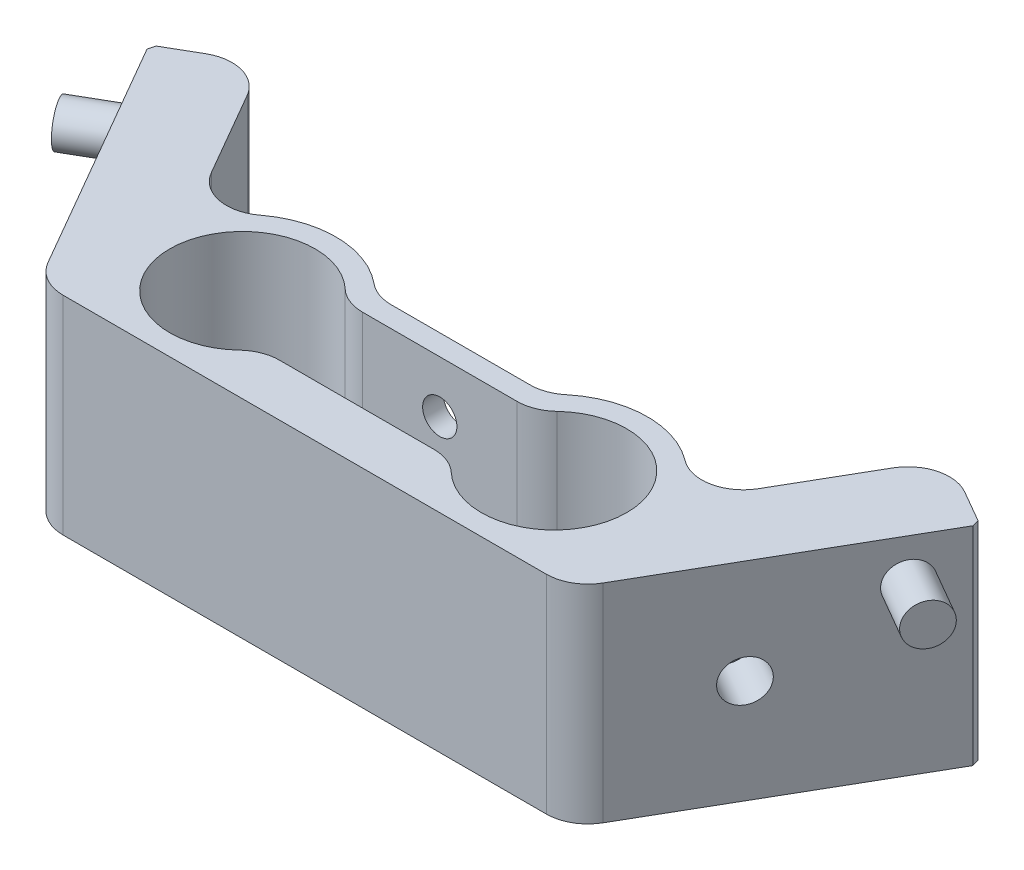
SolidWorks part; units mm, degrees
material "Сплав 2024"
ref_plane "Спереди" through (0, 0, 0) normal (0, 0, 1) x (1, 0, 0)
ref_plane "Сверху" through (0, 0, 0) normal (0, 1, 0) x (1, 0, 0)
ref_plane "Справа" through (0, 0, 0) normal (1, 0, 0) x (0, 0, -1)
sketch "Эскиз1" plane through (0, 0, 0) normal (0, 1, 0) x (1, 0, 0)
  line L0 (0, 0) -> (14.4338, -25)
  line L1 (14.4338, -25) -> (65.5662, -25)
  line L2 (65.5662, -25) -> (80, 0)
  line L3 (80, 0) -> (73.0718, 4)
  line L4 (73.0718, 4) -> (63.3961, -12.7588)
  line L5 (31.7082, -10) -> (48.2918, -10)
  line L6 (16.6039, -12.7588) -> (6.9282, 4)
  line L7 (6.9282, 4) -> (0, 0)
  line L8 (0, 5.2504) -> (0, -36.0928) construction
  line L9 (80, 1.6052) -> (80, -36.8181) construction
  line L10 (40, -7) -> (40, -25) construction
  line L11 (40, -16) -> (80, -16) construction
  line L12 (40, -16) -> (0, -16) construction
  line L13 (25, -16) -> (25, -18.6268) construction
  line L14 (55, -16) -> (55, -18.6268) construction
  circle A0 centre (25, -16) radius 7 construction
  circle A1 centre (55, -16) radius 7 construction
  circle A2 centre (55, -16) radius 9 construction
  circle A3 centre (25, -16) radius 9 construction
  arc A4 (16.6039, -12.7588) -> (31.7082, -10) centre (25, -16) cw
  arc A5 (48.2918, -10) -> (63.3961, -12.7588) centre (55, -16) cw
  dimension "D6" = 14
  dimension "D7" = 14
  dimension "D8" = 15
  dimension "D15" = 9
  dimension "D16" = 9
  dimension "D9" = 2
  dimension "D17" = 15
  dimension "D1" = 80
  dimension "D2" = 30
  dimension "D3" = 30
  dimension "D4" = 8
  dimension "D5" = 8
  dimension "D10" = 15
  dimension "D11" = 9
  dimension "D12" = 2
  dimension "D13" = 25
  dimension "D14" = 40
extrude "Бобышка-Вытянуть1" add sketch "Эскиз1" along normal blind 20
sketch "Эскиз2" plane through (0, 20, 0) normal (0, 1, 0) x (1, 0, 0)
  line L1 (40, -16) -> (0, -16) construction
  line L2 (25, -16) -> (25, -18.6268) construction
  circle A0 centre (25, -16) radius 7
  circle A1 centre (55, -16) radius 7
  dimension "D1" = 14
extrude "Вырез-Вытянуть1" cut sketch "Эскиз2" against normal through all
sketch "Эскиз3" plane through (0, 20, 0) normal (0, 1, 0) x (1, 0, 0)
  line L0 (40, -7) -> (40, -25) construction
  line L1 (25, -12) -> (55, -12)
  line L2 (25, -12) -> (25, -20)
  line L3 (25, -20) -> (55, -20)
  line L4 (55, -12) -> (55, -20)
  line L5 (25, -12) -> (55, -20) construction
  line L6 (25, -20) -> (55, -12) construction
  line L8 (25, -16) -> (25, -18.6268) construction
  point P0 (40, -16)
  dimension "D1" = 8
extrude "Вырез-Вытянуть2" cut sketch "Эскиз3" against normal through all
fillet "Скругление1" radius 4 12 edges at (49.2554, 10, 12) (30.7446, 10, 12) (30.7446, 10, 20) (49.2554, 10, 20) (48.2918, 10, 10) (31.7082, 10, 10) (6.9282, 10, -4) (73.0718, 10, -4) (14.4338, 10, 25) (65.5662, 10, 25) (63.3961, 10, 12.7588) (16.6039, 10, 12.7588)
chamfer "Фаска1" distance 0.5 angle 45 2 edges at (80, 10, 0) (0, 10, 0)
sketch "Эскиз4" plane through (0, 0, 10) normal (0, 0, -1) x (-1, 0, 0)
  line L0 (-40, 20) -> (-40, 0) construction
  line L1 (-46.6934, 20) -> (-33.3066, 20) construction
  line L2 (-40, 0) -> (-80, 0) construction
  line L3 (-46.6934, 15) -> (-33.3066, 15) construction
  line L4 (-46.6934, 20) -> (-46.6934, 0) construction
  line L5 (-33.3066, 0) -> (-33.3066, 20) construction
  line L6 (-46.6934, 5) -> (-33.3066, 5) construction
  line L7 (-40, 0) -> (0, 0) construction
  dimension "D1" = 5
  dimension "D2" = 5
hole_wizard "Отверстие обработанное метчиком M4x0.71" positions "Трехмерный эскиз1" profile "Эскиз5" tap size "M4x0.7" standard "Ansi Metric"
sketch3d "Трехмерный эскиз1"
  line L0 (46.6934, 15, 10) -> (33.3066, 15, 10) construction
  line L1 (46.6934, 5, 10) -> (33.3066, 5, 10) construction
  line L2 (40, 20, 10) -> (40, 0, 10) construction
  point P8 (40, 5, 10)
  point P12 (40, 15, 10)
sketch "Эскиз5" plane through (40, 5, 10) normal (1, 0, 0) x (0, 1, 0)
  line L0 (0, 0) -> (0, 14.4914)
  line L1 (0, 14.4914) -> (1.65, 13.5)
  line L2 (1.65, 13.5) -> (1.65, 0)
  line L5 (1.65, 0) -> (0, 0)
  line L10 (0, 14.4914) -> (-1.65, 13.5) construction
  line L11 (0, -6.35) -> (0, 107.95) construction
  dimension "Диаметр сверла" = 3.3
  dimension "Глубина сверла" = 13.5
  dimension "Угол заточки сверла" = 118
sketch "Эскиз6" plane through (60, 0, 34.641) normal (0.866, 0, 0.5) x (0.5, 0, -0.866)
  line L0 (33.4419, 20) -> (33.4419, 0) construction
  line L1 (13.4419, 20) -> (39.5, 20) construction
  line L2 (13.4419, 0) -> (39.5, 0) construction
  line L3 (13.4419, 20) -> (13.4419, 0) construction
  line L4 (40, 20) -> (40, 0) construction
  line L5 (40, 10) -> (13.4419, 10) construction
  line L6 (23.4419, 20) -> (23.4419, 0) construction
  circle A0 centre (23.4419, 10) radius 2
  dimension "D4" = 4
  dimension "D1" = 20
  dimension "D2" = 6.5581
  dimension "D3" = 10
extrude "Вырез-Вытянуть3" cut sketch "Эскиз6" against normal blind 5
sketch "Эскиз7" plane through (0, 0, 0) normal (-0.866, 0, 0.5) x (0.5, 0, 0.866)
  line L0 (0, 10) -> (26.5581, 10) construction
  line L1 (0, 20) -> (0, 0) construction
  line L2 (26.5581, 0) -> (26.5581, 20) construction
  line L3 (16.5581, 20) -> (16.5581, 0) construction
  line L4 (0.5, 20) -> (26.5581, 20) construction
  line L5 (0.5, 0) -> (26.5581, 0) construction
  circle A0 centre (16.5581, 10) radius 2
  dimension "D2" = 4
  dimension "D1" = 10
extrude "Вырез-Вытянуть4" cut sketch "Эскиз7" against normal blind 5
sketch "Эскиз8" plane through (0, 0, 0) normal (-0.866, 0, 0.5) x (0.5, 0, 0.866)
  line L0 (5, 0) -> (5, 20) construction
  line L2 (0, 16) -> (26.5581, 16) construction
  line L5 (0, 20) -> (0, 0) construction
  line L6 (0.5, 20) -> (26.5581, 20) construction
  circle A0 centre (5, 16) radius 2
  dimension "D3" = 4
  dimension "D1" = 5
  dimension "D2" = 4
extrude "Бобышка-Вытянуть2" add sketch "Эскиз8" along normal blind 5
sketch "Эскиз9" plane through (60, 0, 34.641) normal (0.866, 0, 0.5) x (0.5, 0, -0.866)
  line L0 (35, 20) -> (35, 0) construction
  line L1 (13.4419, 20) -> (39.5, 20) construction
  line L2 (13.4419, 0) -> (39.5, 0) construction
  line L3 (13.4419, 16) -> (40, 16) construction
  line L4 (13.4419, 20) -> (13.4419, 0) construction
  line L5 (40, 20) -> (40, 0) construction
  circle A0 centre (35, 16) radius 2
  dimension "D3" = 4
  dimension "D1" = 4
  dimension "D2" = 5
extrude "Бобышка-Вытянуть3" add sketch "Эскиз9" along normal blind 5
